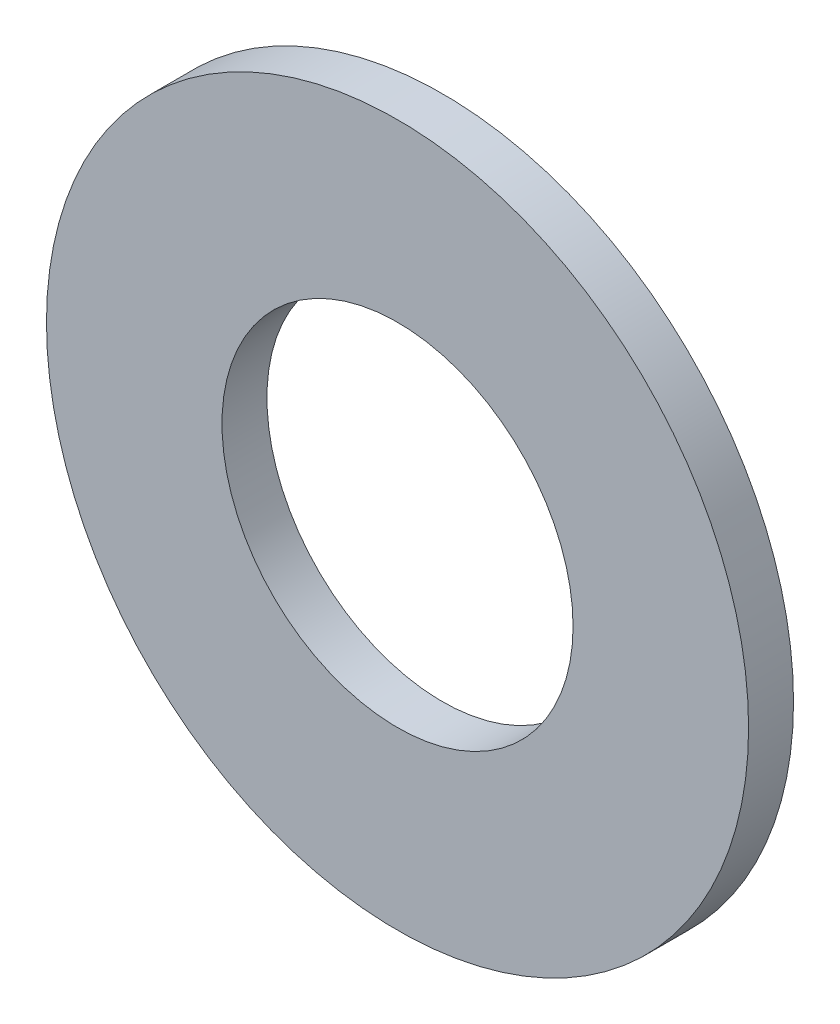
SolidWorks part; units mm, degrees
material "Alloy Steel"
ref_plane "Front Plane" through (0, 0, 0) normal (0, 0, 1) x (1, 0, 0)
ref_plane "Top Plane" through (0, 0, 0) normal (0, 1, 0) x (1, 0, 0)
ref_plane "Right Plane" through (0, 0, 0) normal (1, 0, 0) x (0, 0, -1)
sketch "Sketch1" plane through (0, 0, 0) normal (0, 0, 1) x (1, 0, 0)
  circle A0 centre (0, 0) radius 1.9844
  circle A1 centre (0, 0) radius 3.9688
  dimension "ID" = 3.9688
  dimension "OD" = 7.9375
extrude "Extrude1" add sketch "Sketch1" against normal blind 0.508
